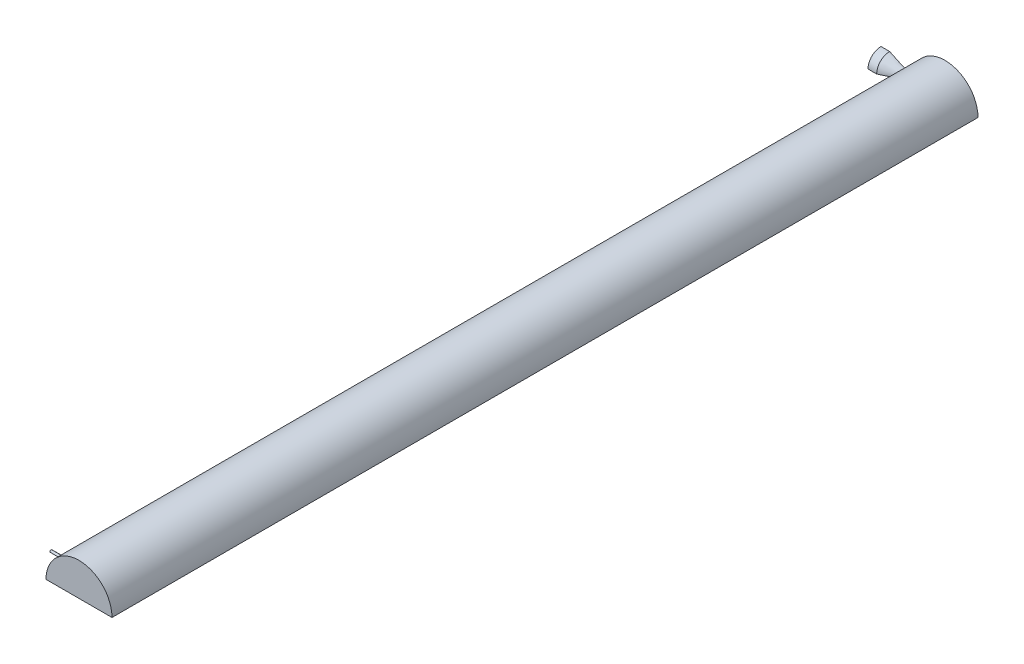
SolidWorks part; units mm, degrees
ref_plane "Front Plane" through (0, 0, 0) normal (0, 0, 1) x (1, 0, 0)
ref_plane "Top Plane" through (0, 0, 0) normal (0, 1, 0) x (1, 0, 0)
ref_plane "Right Plane" through (0, 0, 0) normal (1, 0, 0) x (0, 0, -1)
sketch "Sketch2" plane through (0, 0, 0) normal (0, 0, 1) x (1, 0, 0)
  line L0 (-0.6542, 15.02) -> (-10.6542, 15.02)
  line L1 (0, 0) -> (25.4, 0)
  line L3 (0, 0) -> (-10.6542, 0)
  line L4 (-10.6542, 15.02) -> (-10.6542, 0)
  line L5 (25.4, 4.5) -> (35.4, 4.5)
  line L6 (35.4, 4.5) -> (35.4, 0)
  line L7 (35.4, 0) -> (25.4, 0)
  spline S0 degree 4 poles (-3.1933, 16.2453) (-2.6483, 15.9818) (-1.017, 15.1947) (-0.2611, 14.8302) (2.741, 13.3865) (4.3471, 12.6191) (6.7016, 11.496) (8.6069, 10.5959) (10.7909, 9.5706) (12.8108, 8.6376) (14.9441, 7.6698) (16.9508, 6.7919) (18.7556, 6.0442) (20.2388, 5.4862) (21.3942, 5.1036) (22.2156, 4.8709) (22.897, 4.7103) (23.4645, 4.6056) (23.9541, 4.5381) (24.3543, 4.5036) (24.6693, 4.4888) (24.9186, 4.4854) (25.1247, 4.4882) (25.3381, 4.4959) (25.4828, 4.5045) (25.721, 4.5241) (25.9474, 4.5492) (26.1677, 4.5804) (26.3997, 4.6194) (26.7077, 4.6797) (27.1217, 4.7773) (27.4707, 4.8773) (27.7551, 4.9689) (27.9139, 5.0231) knots 0 0 0 0 0 0.083771 0.152014 0.220257 0.2885 0.356743 0.424986 0.493229 0.561472 0.629715 0.697958 0.757157 0.791278 0.819344 0.841894 0.858955 0.874283 0.887932 0.900719 0.906406 0.912093 0.917779 0.923466 0.929945 0.936423 0.942902 0.94938 0.956926 0.964472 0.980061 1 1 1 1 1 construction
  spline S1 degree 4 poles (-0.6542, 15.02) (-0.2198, 14.8107) (0.6106, 14.411) (2.741, 13.3865) (4.3471, 12.6191) (6.7016, 11.496) (8.6069, 10.5959) (10.7909, 9.5706) (12.8108, 8.6376) (14.9441, 7.6698) (16.9508, 6.7919) (18.7556, 6.0442) (20.2388, 5.4862) (21.3942, 5.1036) (22.2156, 4.8709) (22.897, 4.7103) (23.4645, 4.6056) (23.9541, 4.5381) (24.3543, 4.5036) (24.6693, 4.4888) (24.9186, 4.4854) (25.1247, 4.4882) (25.2794, 4.4938) (25.3599, 4.4977) (25.4, 4.5) knots 0.083771 0.083771 0.083771 0.083771 0.083771 0.152014 0.220257 0.2885 0.356743 0.424986 0.493229 0.561472 0.629715 0.697958 0.757157 0.791278 0.819344 0.841894 0.858955 0.874283 0.887932 0.900719 0.906406 0.912093 0.917779 0.923466 0.923466 0.923466 0.923466 0.923466
  point P8 (0, 0)
  point P12 (0, 0)
  point P13 (0, 0)
  point P14 (0, 0)
  point P15 (0, 0)
  dimension "D1" = 10.6542
  dimension "D2" = 15.02
  dimension "D3" = 4.5
  dimension "D4" = 25.4
  dimension "D5" = 10
revolve "Revolve3" add sketch "Sketch2" angle 90 about L1
sketch "TempLine" plane through (0, 0, 0) normal (0, 0, -1) x (-1, 0, 0)
  line L0 (-25.4, 4.5) -> (-25.4, 0)
  line L1 (10.6542, 0) -> (-35.4, 0) construction
sketch "Sketch11" plane through (0, 0, 0) normal (0, 0, 1) x (1, 0, 0)
  line L0 (25.1333, 0) -> (101.3333, 0)
  arc A0 (25.1333, 0) -> (101.3333, 0) centre (63.2333, 0) cw
  point P5 (0, 0)
  point P7 (0, 0)
  dimension "D2" = 38.1
  dimension "D1" = 76.2
extrude "Boss-Extrude2" add sketch "Sketch11" along normal blind 1000 contours A0 L0
sketch "Sketch16" plane through (0, 0, 0) normal (1, 0, 0) x (0, 0, -1)
  line L0 (-1000, 0) -> (-4.4894, 0) construction
  line L1 (-967.5038, 0) -> (-970.5078, 0)
  arc A0 (-970.5078, 0) -> (-967.5038, 0) centre (-969.0058, 0) cw
  dimension "D1" = 1.502
extrude "Boss-Extrude4" add sketch "Sketch16" along normal blind 50 contours A0 L1
